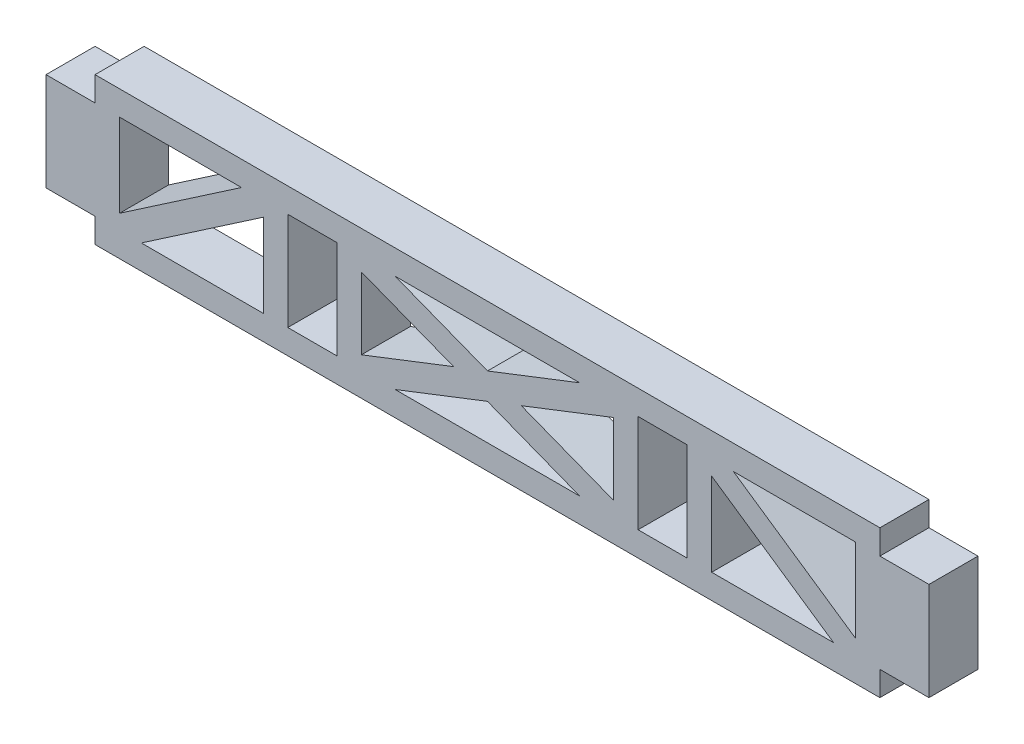
SolidWorks part; units mm, degrees
ref_plane "Front Plane" through (0, 0, 0) normal (0, 0, 1) x (1, 0, 0)
ref_plane "Top Plane" through (0, 0, 0) normal (0, 1, 0) x (1, 0, 0)
ref_plane "Right Plane" through (0, 0, 0) normal (1, 0, 0) x (0, 0, -1)
sketch "Sketch1" plane through (0, 0, 0) normal (0, 0, 1) x (1, 0, 0)
  line L0 (-50.8, -6.35) -> (-50.8, 6.35) construction
  line L1 (-50.8, -9.525) -> (50.8, -9.525)
  line L2 (-50.8, -9.525) -> (-50.8, -6.35)
  line L3 (-50.8, 9.525) -> (50.8, 9.525)
  line L4 (50.8, -9.525) -> (50.8, -6.35)
  line L5 (-50.8, -9.525) -> (50.8, 9.525) construction
  line L6 (-50.8, 9.525) -> (50.8, -9.525) construction
  line L7 (-50.8, 6.35) -> (-57.15, 6.35)
  line L8 (-50.8, 6.35) -> (-50.8, -6.35) construction
  line L9 (-50.8, -6.35) -> (-57.15, -6.35)
  line L10 (-57.15, 6.35) -> (-57.15, -6.35)
  line L11 (50.8, 6.35) -> (57.15, 6.35)
  line L12 (50.8, 6.35) -> (50.8, -6.35) construction
  line L13 (50.8, -6.35) -> (57.15, -6.35)
  line L14 (57.15, 6.35) -> (57.15, -6.35)
  line L15 (-50.8, 6.35) -> (-50.8, 9.525)
  line L16 (50.8, -6.35) -> (50.8, 6.35) construction
  line L17 (50.8, 6.35) -> (50.8, 9.525)
  line L18 (0, -55) -> (0, 55) construction
  line L19 (-25.85, 6.35) -> (-19.5, 6.35)
  line L20 (-25.85, 6.35) -> (-25.85, -6.35)
  line L21 (-25.85, -6.35) -> (-19.5, -6.35)
  line L22 (-19.5, 6.35) -> (-19.5, -6.35)
  line L23 (25.85, -6.35) -> (19.5, -6.35)
  line L24 (19.5, 6.35) -> (19.5, -6.35)
  line L25 (25.85, 6.35) -> (19.5, 6.35)
  line L26 (25.85, 6.35) -> (25.85, -6.35)
  point P0 (0, 0)
  point P15 (57.15, 0)
  point P16 (-57.15, 0)
  dimension "D1" = 101.6
  dimension "D2" = 6.35
  dimension "D3" = 12.7
  dimension "D4" = 3.175
  dimension "D5" = 39
extrude "Boss-Extrude1" add sketch "Sketch1" along normal mid plane 6.35
sketch "Sketch2" plane through (0, 0, 3.175) normal (0, 0, 1) x (1, 0, 0)
  line L0 (-1000, 0) -> (49000, 0) construction
  line L1 (-47.625, 6.35) -> (-47.625, -6.35)
  line L2 (-47.625, -6.35) -> (-29.025, -6.35)
  line L3 (-29.025, -6.35) -> (-29.025, 6.35)
  line L4 (-29.025, 6.35) -> (-47.625, 6.35)
  line L5 (-50.8, 6.35) -> (-57.15, 6.35) construction
  line L6 (-50.8, 9.525) -> (-50.8, 6.35) construction
  line L7 (-31.8403, 6.35) -> (-47.625, -4.4277)
  line L8 (-50.8, 6.35) -> (-47.625, 6.35) construction
  line L9 (16.325, -6.35) -> (-16.325, -6.35)
  line L10 (16.325, -6.35) -> (16.325, 6.35)
  line L11 (16.325, 6.35) -> (-16.325, 6.35)
  line L12 (-16.325, -6.35) -> (-16.325, 6.35)
  line L13 (16.325, -6.35) -> (-16.325, 6.35) construction
  line L14 (16.325, 6.35) -> (-16.325, -6.35) construction
  line L15 (-29.025, 6.35) -> (-25.85, 6.35) construction
  line L16 (-19.5, 6.35) -> (-16.325, 6.35) construction
  line L17 (16.325, 6.35) -> (19.5, 6.35) construction
  line L18 (-47.625, 6.35) -> (-29.025, -6.35) construction
  line L19 (-29.025, 6.35) -> (-47.625, -6.35) construction
  line L20 (-29.025, 4.4277) -> (-44.8097, -6.35)
  line L21 (-29.9202, 7.661) -> (-48.5202, -5.039) construction
  line L22 (-28.1298, 5.039) -> (-46.7298, -7.661) construction
  line L23 (16.325, -4.6466) -> (-11.9459, 6.35)
  line L24 (11.9459, 6.35) -> (-16.325, -4.6466)
  line L25 (11.9459, -6.35) -> (-16.325, 4.6466)
  line L26 (16.325, 4.6466) -> (-11.9459, -6.35)
  line L27 (16.9005, -4.8705) -> (-15.7495, 7.8295) construction
  line L28 (15.7495, -7.8295) -> (-16.9005, 4.8705) construction
  line L29 (15.7495, 7.8295) -> (-16.9005, -4.8705) construction
  line L30 (16.9005, 4.8705) -> (-15.7495, -7.8295) construction
  line L31 (0, -3.4925) -> (0, 3.4925) construction
  line L32 (31.8403, 6.35) -> (47.625, -4.4277)
  line L33 (29.025, 4.4277) -> (44.8097, -6.35)
  line L34 (29.025, -6.35) -> (29.025, 6.35)
  line L35 (47.625, -6.35) -> (29.025, -6.35)
  line L36 (47.625, 6.35) -> (47.625, -6.35)
  line L37 (29.025, 6.35) -> (47.625, 6.35)
  point P9 (-47.625, 0)
  point P14 (0, 0)
  dimension "D1" = 3.175
  dimension "D2" = 1.5875
  dimension "D3" = 1.5875
  dimension "D4" = 1.5875
  dimension "D5" = 1.5875
extrude "Cut-Extrude1" cut sketch "Sketch2" against normal through all contours L7 L4 L1 | L3 L20 L2 | L24 L25 L12 | L24 L11 L23 | L10 L26 L23 | L25 L26 L9 | L35 L33 L34 | L37 L32 L36
